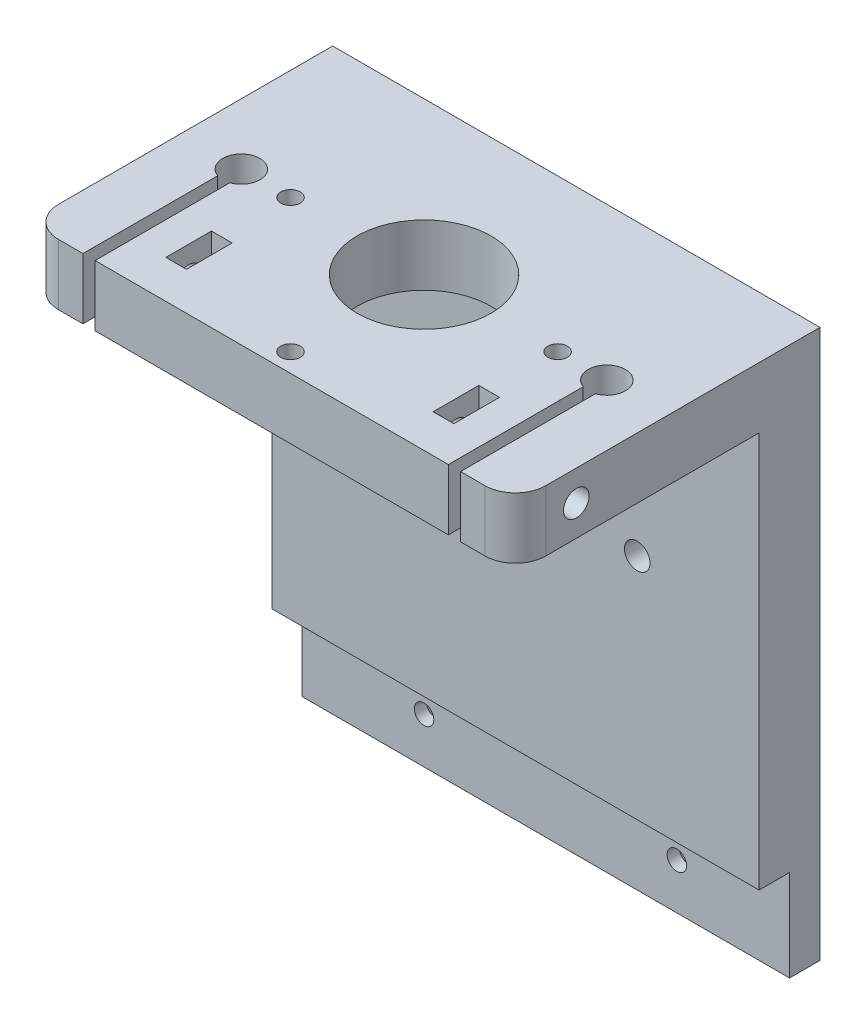
SolidWorks part; units mm, degrees
ref_plane "前基準面" through (0, 0, 0) normal (0, 0, 1) x (1, 0, 0)
ref_plane "上基準面" through (0, 0, 0) normal (0, 1, 0) x (1, 0, 0)
ref_plane "右基準面" through (0, 0, 0) normal (1, 0, 0) x (0, 0, -1)
sketch "草圖1" plane through (0, 0, 0) normal (0, 0, 1) x (1, 0, 0)
  line L1 (-40, 75) -> (40, 75)
  line L2 (-40, 75) -> (-40, -75)
  line L3 (-40, -75) -> (40, -75)
  line L4 (40, 75) -> (40, -75)
  line L5 (-40, 75) -> (40, -75) construction
  line L6 (-40, -75) -> (40, 75) construction
  point P0 (0, 0)
  dimension "D1" = 150
  dimension "D2" = 80
extrude "填料-伸長1" add sketch "草圖1" along normal blind 10
sketch "草圖4" plane through (0, -75, 0) normal (0, -1, 0) x (1, 0, 0)
  line L0 (0, 0) -> (0, 37.8464) construction
  line L1 (-40, 10) -> (40, 10)
  line L2 (-40, 10) -> (-40, 50)
  line L3 (-40, 50) -> (-31, 50)
  line L4 (40, 10) -> (40, 50)
  line L5 (-29, 50) -> (-6, 50)
  line L7 (-31, 50) -> (-31, 27.8814)
  line L9 (-29, 50) -> (-29, 27.8814)
  line L10 (29, 50) -> (29, 27.8814)
  line L11 (31, 50) -> (31, 27.8814)
  line L12 (31, 50) -> (40, 50)
  line L13 (-30, 25) -> (30, 25) construction
  line L14 (-6, 49) -> (-6, 50)
  line L16 (6, 49) -> (6, 50)
  line L17 (6, 50) -> (29, 50)
  arc A0 (-31, 27.8814) -> (-29, 27.8814) centre (-30, 25) ccw
  arc A1 (29, 27.8814) -> (31, 27.8814) centre (30, 25) ccw
  circle A2 centre (0, 25) radius 11.25
  circle A3 centre (0, 25) radius 5
  arc A4 (-6, 49) -> (6, 49) centre (0, 49) ccw
  point P13 (-30, 50)
  line M18 (40, 10) -> (-40, 10)
  dimension "D2" = 6.1
  dimension "D5" = 22.5
  dimension "D6" = 10
  dimension "D7" = 12
  dimension "D1" = 40
  dimension "D3" = 15
  dimension "D4" = 10
  dimension "D8" = 1
  dimension "D9" = 60
extrude "填料-伸長3" add sketch "草圖4" against normal blind 10 contours A4 L14 L5 L9 A0 L7 L3 L2 L4 L12 L11 A1 L10 L17 L16 A2 M18
sketch "草圖5" plane through (0, -75, 0) normal (0, -1, 0) x (1, 0, 0)
  circle A0 centre (0, 25) radius 11.25
  circle A1 centre (0, 25) radius 5
  dimension "D1" = 10
  dimension "D2" = 22.5
extrude "填料-伸長4" add sketch "草圖5" against normal blind 4
sketch "草圖6" plane through (40, 0, 0) normal (1, 0, 0) x (0, 0, -1)
  line L0 (-50, -65) -> (-50, -75) construction
  circle A0 centre (-40, -70) radius 2.1
  dimension "D2" = 4.2
  dimension "D1" = 10
extrude "除料-伸長1" cut sketch "草圖6" against normal blind 24
sketch "草圖7" plane through (0, -75, 0) normal (0, -1, 0) x (1, 0, 0)
  line L0 (16, 40) -> (21.9431, 40) construction
  line L1 (16, 37.9) -> (16, 42.1) construction
  line L2 (21.9431, 40) -> (0, 24.9665) construction
  line L3 (0, 24.9665) -> (0, 53.0789) construction
  line L4 (-20.2431, 36.25) -> (-20.2431, 43.75)
  line L5 (20.2431, 36.25) -> (23.6431, 36.25)
  line L6 (20.2431, 36.25) -> (20.2431, 43.75)
  line L7 (20.2431, 43.75) -> (23.6431, 43.75)
  line L8 (23.6431, 36.25) -> (23.6431, 43.75)
  line L9 (20.2431, 36.25) -> (23.6431, 43.75) construction
  line L10 (20.2431, 43.75) -> (23.6431, 36.25) construction
  line L11 (-20.2431, 36.25) -> (-23.6431, 36.25)
  line L12 (-23.6431, 36.25) -> (-23.6431, 43.75)
  line L13 (-20.2431, 43.75) -> (-23.6431, 43.75)
  dimension "D1" = 3.4
  dimension "D2" = 7.5
extrude "除料-伸長2" cut sketch "草圖7" against normal blind 24
sketch "草圖8" plane through (-40, 0, 0) normal (-1, 0, 0) x (0, 0, 1)
  circle A0 centre (40, -70) radius 2.1
extrude "除料-伸長3" cut sketch "草圖8" against normal blind 24
sketch "草圖9" plane through (0, 75, 0) normal (0, 1, 0) x (1, 0, 0)
  line L0 (0, 0) -> (0, -54.0504) construction
  line L1 (-40, -10) -> (40, -10)
  line L2 (-40, -10) -> (-40, -50)
  line L3 (-40, -50) -> (40, -50)
  line L4 (40, -10) -> (40, -50)
  line L6 (-21.9203, -25) -> (0, -46.9203) construction
  line L7 (-21.9203, -25) -> (0, -3.0797) construction
  line L8 (0, -3.0797) -> (21.9203, -25) construction
  line L9 (0, -46.9203) -> (21.9203, -25) construction
  line L10 (-21.9203, -25) -> (21.9203, -25) construction
  line L11 (0, -3.0797) -> (0, -46.9203) construction
  circle A0 centre (0, -25) radius 5 construction
  circle A1 centre (0, -25) radius 5 construction
  circle A2 centre (0, -25) radius 11
  circle A3 centre (-21.9203, -25) radius 1.6
  circle A4 centre (0, -46.9203) radius 1.6
  circle A5 centre (21.9203, -25) radius 1.6
  dimension "D1" = 22
  dimension "D3" = 3.2
  dimension "D2" = 31
extrude "填料-伸長5" add sketch "草圖9" against normal blind 10 contours L2 L1 L4 L3 | A2 | A3 | A5 | A4
fillet "圓角1" radius 5 4 edges at (-40, -70, 50) (-40, 70, 50) (40, -70, 50) (40, 70, 50)
sketch "草圖10" plane through (0, 75, 0) normal (0, 1, 0) x (1, 0, 0)
  line L0 (-35, -50) -> (35, -50) construction
  line L1 (-30.9921, -72.1172) -> (-29, -72.1172)
  line L2 (-30.9921, -72.1172) -> (-30.9921, -27.8841)
  line L4 (-29, -72.1172) -> (-29, -27.8814)
  line L5 (-30.9921, -72.1172) -> (-29, -27.8814) construction
  line L6 (-30.9921, -27.8841) -> (-29, -72.1172) construction
  line L8 (29.0016, -72.1183) -> (31, -72.1183)
  line L9 (29.0016, -72.1183) -> (29.0016, -27.882)
  line L11 (31, -72.1183) -> (31, -27.8814)
  line L12 (29.0016, -72.1183) -> (31, -27.8814) construction
  line L13 (29.0016, -27.882) -> (31, -72.1183) construction
  line L14 (-23.6431, -36.25) -> (-20.2431, -36.25)
  line L15 (-23.6431, -36.25) -> (-23.6431, -43.75)
  line L16 (-23.6431, -43.75) -> (-20.2431, -43.75)
  line L17 (-20.2431, -36.25) -> (-20.2431, -43.75)
  line L18 (20.2431, -36.25) -> (23.6431, -36.25)
  line L19 (20.2431, -36.25) -> (20.2431, -43.75)
  line L20 (20.2431, -43.75) -> (23.6431, -43.75)
  line L21 (23.6431, -36.25) -> (23.6431, -43.75)
  arc A0 (-29, -27.8814) -> (-30.9921, -27.8841) centre (-30, -25) ccw
  arc A1 (31, -27.8814) -> (29.0016, -27.882) centre (30, -25) ccw
  point P6 (-29.9961, -50)
  point P14 (30.0008, -50)
extrude "除料-伸長5" cut sketch "草圖10" against normal blind 10 contours L2 A0 L4 L1 | L15 L14 L17 L16 | L19 L18 L21 L20 | L9 A1 L11 L8
sketch "草圖11" plane through (40, 0, 0) normal (1, 0, 0) x (0, 0, -1)
  line L0 (-40, -70) -> (-40, 84.814) construction
  circle A0 centre (-40, 70) radius 2.1
  dimension "D1" = 4.2
extrude "除料-伸長6" cut sketch "草圖11" against normal blind 24
sketch "草圖12" plane through (-40, 0, 0) normal (-1, 0, 0) x (0, 0, 1)
  circle A0 centre (40, 70) radius 2.1
extrude "除料-伸長7" cut sketch "草圖12" against normal blind 24
sketch "草圖14" plane through (0, -75, 0) normal (0, -1, 0) x (1, 0, 0)
  line L0 (0, 49) -> (0, 57.7275) construction
  line L1 (-12, 53.5876) -> (-12, 37.2144) construction
  line L2 (-29, 50) -> (-6, 50) construction
  line L3 (-14, 45) -> (-10, 45)
  line L4 (-14, 45) -> (-14, 47)
  line L5 (-14, 47) -> (-10, 47)
  line L6 (-10, 45) -> (-10, 47)
  line L7 (-14, 45) -> (-10, 47) construction
  line L8 (-14, 47) -> (-10, 45) construction
  line L9 (14, 45) -> (10, 45)
  line L10 (10, 45) -> (10, 47)
  line L11 (14, 47) -> (10, 47)
  line L12 (14, 45) -> (14, 47)
  point P6 (-12, 46)
  dimension "D1" = 4
  dimension "D2" = 2
  dimension "D3" = 12
  dimension "D4" = 4
extrude "除料-伸長9" cut sketch "草圖14" against normal blind 10
sketch "草圖16" plane through (0, 0, 10) normal (0, 0, 1) x (1, 0, 0)
  line L1 (-20, -37.5) -> (20, -37.5) construction
  line L2 (-20, -37.5) -> (-20, 37.5) construction
  line L3 (-20, 37.5) -> (20, 37.5) construction
  line L4 (20, -37.5) -> (20, 37.5) construction
  line L5 (-20, -37.5) -> (20, 37.5) construction
  line L6 (-20, 37.5) -> (20, -37.5) construction
  circle A0 centre (-20, 37.5) radius 2.1
  circle A1 centre (20, 37.5) radius 2.1
  circle A2 centre (20, -37.5) radius 2.1
  circle A3 centre (-20, -37.5) radius 2.1
  point P0 (0, 0)
  dimension "D3" = 4.2
  dimension "D1" = 40
  dimension "D2" = 75
extrude "除料-伸長10" cut sketch "草圖16" against normal through all
sketch "草圖17" plane through (40, 0, 0) normal (1, 0, 0) x (0, 0, -1)
  line L0 (-10, -65) -> (-10, 65) construction
  line L1 (-10, -15) -> (-13, -15)
  line L2 (-13, -15) -> (-13, 0)
  line L3 (-13, 0) -> (-5, 0)
  line L4 (-5, 0) -> (-5, -15)
  line L5 (-5, -15) -> (0, -15)
  line L6 (0, -75) -> (0, 75) construction
  line L7 (-10, -65) -> (-45, -65) construction
  line L10 (-50, -65) -> (-50, -75)
  line L11 (-50, -75) -> (0, -75)
  line L12 (0, -75) -> (0, -15)
  line L13 (-10, -15) -> (-10, -65)
  line L15 (-50, -65) -> (-10, -65)
  dimension "D1" = 50
  dimension "D2" = 15
  dimension "D3" = 8
  dimension "D4" = 3
extrude "除料-伸長12" cut sketch "草圖17" against normal through all
sketch "草圖19" plane through (0, 0, 0) normal (0, 0, -1) x (-1, 0, 0)
  line L0 (-40, 0) -> (-40, -15) construction
  line L1 (-40, -15) -> (-40, -7.5) construction
  line L2 (-40, -7.5) -> (40, -7.5) construction
  line L3 (40, 75) -> (40, -15) construction
  line L4 (40, -7.5) -> (0, 0) construction
  line L5 (40, 0) -> (-40, 0) construction
  line L6 (0, 0) -> (0, -15) construction
  line L7 (40, -15) -> (-40, -15) construction
  line L9 (-18.0365, -7.5) -> (-19.7685, -4.5)
  line L10 (-19.7685, -4.5) -> (-23.2326, -4.5)
  line L11 (-23.2326, -4.5) -> (-24.9647, -7.5)
  line L12 (-24.9647, -7.5) -> (-23.2326, -10.5)
  line L13 (-23.2326, -10.5) -> (-19.7685, -10.5)
  line L14 (-19.7685, -10.5) -> (-18.0365, -7.5)
  line L15 (23.4641, -7.5) -> (21.7321, -4.5)
  line L16 (21.7321, -4.5) -> (18.2679, -4.5)
  line L17 (18.2679, -4.5) -> (16.5359, -7.5)
  line L18 (16.5359, -7.5) -> (18.2679, -10.5)
  line L19 (18.2679, -10.5) -> (21.7321, -10.5)
  line L20 (21.7321, -10.5) -> (23.4641, -7.5)
  circle A0 centre (-21.5006, -7.5) radius 3 construction
  circle A1 centre (20, -7.5) radius 3 construction
  dimension "D1" = 6
  dimension "D2" = 21.5006
  dimension "D3" = 6
  dimension "D4" = 20
extrude "除料-伸長13" cut sketch "草圖19" against normal blind 3
sketch "草圖20" plane through (0, 0, 0) normal (0, 0, -1) x (-1, 0, 0)
  line L0 (-19.7685, -4.5) -> (-23.2326, -10.5) construction
  line L1 (-23.2326, -10.5) -> (-19.7685, -10.5) construction
  line L2 (-19.7685, -10.5) -> (-23.2326, -4.5) construction
  line L3 (-19.7685, -4.5) -> (-23.2326, -4.5) construction
  line L4 (-19.7685, -4.5) -> (-23.2326, -4.5) construction
  line L5 (-23.2326, -4.5) -> (18.2679, -4.5) construction
  line L6 (18.2679, -4.5) -> (21.7321, -10.5) construction
  line L7 (21.7321, -10.5) -> (18.2679, -10.5) construction
  line L8 (18.2679, -10.5) -> (21.7321, -4.5) construction
  circle A0 centre (-21.5006, -7.5) radius 1.6
  circle A1 centre (20, -7.5) radius 1.6
  dimension "D1" = 3.2
  dimension "D2" = 3.2
extrude "除料-伸長15" cut sketch "草圖20" against normal blind 20
